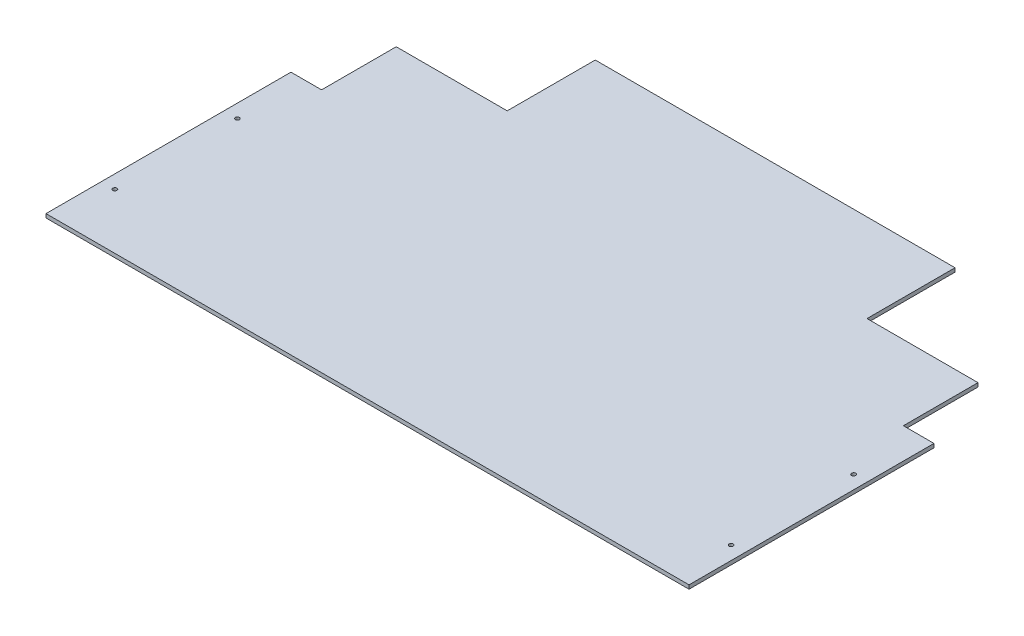
SolidWorks part; units mm, degrees
material "PE High Density"
ref_plane "Front Plane" through (0, 0, 0) normal (0, 0, 1) x (1, 0, 0)
ref_plane "Top Plane" through (0, 0, 0) normal (0, 1, 0) x (1, 0, 0)
ref_plane "Right Plane" through (0, 0, 0) normal (1, 0, 0) x (0, 0, -1)
sketch "Sketch1" plane through (0, 0, 0) normal (0, 1, 0) x (1, 0, 0)
  line L0 (1016, 406.4) -> (1066.8, 406.4)
  line L1 (0, 0) -> (1066.8, 0)
  line L2 (0, 0) -> (0, 406.4)
  line L3 (0, 406.4) -> (50.8, 406.4)
  line L4 (1066.8, 0) -> (1066.8, 406.4)
  line L6 (234.95, 530.225) -> (234.95, 676.275)
  line L7 (234.95, 676.275) -> (831.85, 676.275)
  line L8 (831.85, 530.225) -> (831.85, 676.275)
  line L12 (234.95, 530.225) -> (50.8, 530.225)
  line L13 (50.8, 406.4) -> (50.8, 530.225)
  line L16 (831.85, 530.225) -> (1016, 530.225)
  line L17 (1016, 406.4) -> (1016, 530.225)
  circle A2 centre (22.225, 92.075) radius 3.3734
  circle A3 centre (1044.575, 92.075) radius 3.3734
  circle A4 centre (22.225, 295.275) radius 3.3734
  circle A5 centre (1044.575, 295.275) radius 3.3734
  dimension "D16" = 92.075
  dimension "D11" = 6.7469
  dimension "D1" = 1066.8
  dimension "D2" = 406.4
  dimension "D3" = 596.9
  dimension "D4" = 234.95
  dimension "D5" = 676.275
  dimension "D6" = 50.8
  dimension "D7" = 50.8
  dimension "D8" = 146.05
  dimension "D9" = 146.05
  dimension "D10" = 203.2
  dimension "D15" = 22.225
  dimension "D18" = 22.225
extrude "Boss-Extrude1" add sketch "Sketch1" along normal blind 6.35
sketch "Sketch3" plane through (0, 6.35, 0) normal (0, 1, 0) x (1, 0, 0)
  line L0 (0, 0) -> (1066.8, 0) construction
  line L1 (0, 406.4) -> (0, 0) construction
  line L2 (234.95, 530.225) -> (50.8, 530.225) construction
  line L3 (50.8, 530.225) -> (50.8, 406.4) construction
  line L4 (59.3115, 45.8775) -> (771.914, 277.4161) construction
  line L5 (134.9375, 487.7489) -> (219.4864, 515.2205) construction
  line L6 (0, 406.4) -> (0, 0) construction
  circle A0 centre (134.9375, 487.7489) radius 2.4575
  circle A1 centre (219.4864, 515.2205) radius 2.4575
  circle A2 centre (59.3115, 45.8775) radius 2.4575
  circle A3 centre (296.8457, 123.057) radius 2.4574
  circle A4 centre (534.3799, 200.2365) radius 2.4575
  circle A5 centre (771.914, 277.4161) radius 2.4575
  circle A6 centre (854.075, 309.0545) radius 2.4575
  circle A7 centre (854.075, 486.8545) radius 2.4575
  circle A8 centre (88.9, 492.125) radius 22.225
  dimension "D6" = 486.8545
  dimension "D16" = 4.9149
  dimension "D17" = 44.45
  dimension "D1" = 45.8775
  dimension "D2" = 18
  dimension "D3" = 249.7582
  dimension "D4" = 249.7582
  dimension "D5" = 309.0545
  dimension "D7" = 59.3115
  dimension "D8" = 249.7582
  dimension "D9" = 88.9
  dimension "D10" = 396.875
  dimension "D11" = 854.075
  dimension "D12" = 134.9375
  dimension "D18" = 38.1
  dimension "D19" = 38.1
sketch "Sketch2" plane through (0, 6.35, 0) normal (0, 1, 0) x (1, 0, 0)
  line L0 (0, 0) -> (1066.8, 0) construction
  line L1 (310.5788, 0) -> (149.225, 0)
  line L4 (149.225, 0) -> (149.225, 95.25)
  line L5 (310.5788, 0) -> (247.65, 193.675)
  line L6 (247.65, 193.675) -> (157.0619, 164.2411)
  line L8 (0, 406.4) -> (0, 0) construction
  line L10 (157.0619, 164.2411) -> (171.0336, 121.2405)
  line L11 (171.0336, 121.2405) -> (149.225, 95.25)
  dimension "D1" = 247.65
  dimension "D2" = 149.225
  dimension "D3" = 72
  dimension "D4" = 122
  dimension "D5" = 95.25
  dimension "D6" = 193.675
  dimension "D8" = 95.25
sketch "Sketch4" plane through (0, 6.35, 0) normal (0, 1, 0) x (1, 0, 0)
  point P0 (22.225, 92.075)
  point P5 (1044.575, 92.075)
